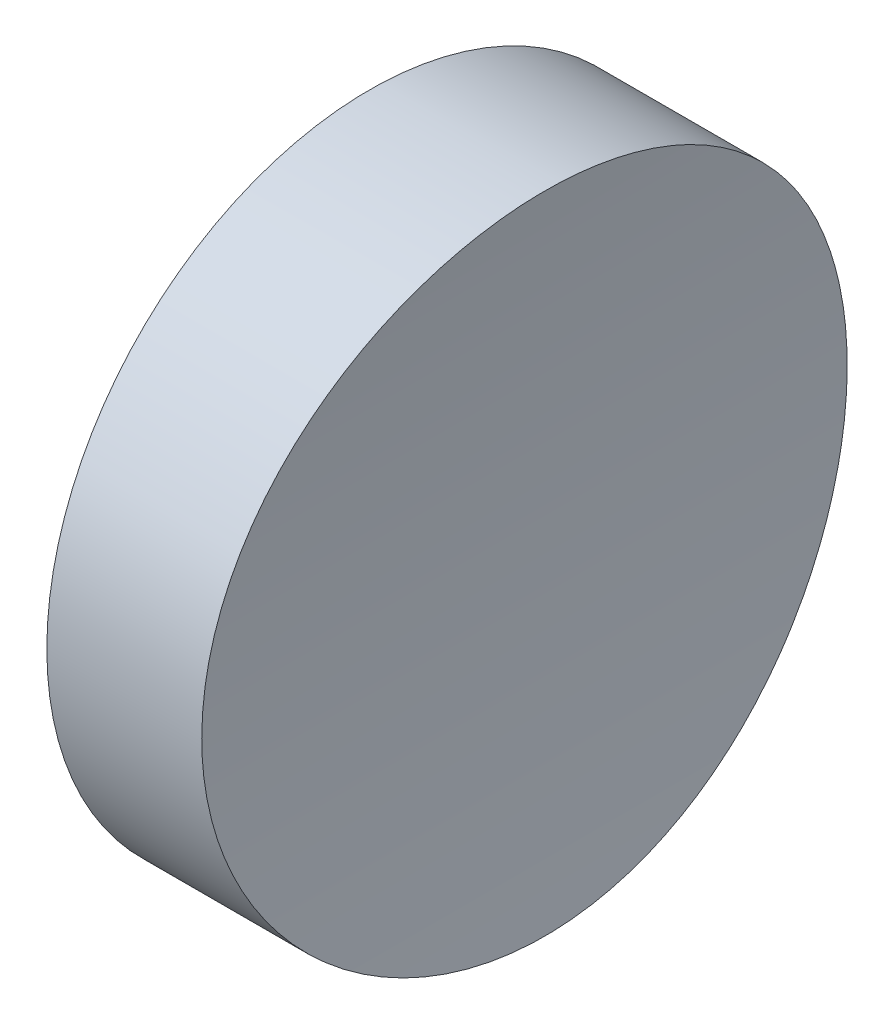
SolidWorks part; units mm, degrees
ref_plane "前视基准面" through (0, 0, 0) normal (0, 0, 1) x (1, 0, 0)
ref_plane "上视基准面" through (0, 0, 0) normal (0, 1, 0) x (1, 0, 0)
ref_plane "右视基准面" through (0, 0, 0) normal (1, 0, 0) x (0, 0, -1)
sketch "草图1" plane through (0, 0, 0) normal (1, 0, 0) x (0, 0, -1)
  circle A0 centre (0, 0) radius 6.25
  dimension "D1" = 12.5
extrude "凸台-拉伸1" add sketch "草图1" along normal blind 10
sketch "草图2" plane through (0, 0, 0) normal (0, 0, 1) x (1, 0, 0)
  line L0 (0, 0) -> (53, 0) construction
  line L1 (0, 0) -> (3, 0) construction
  circle A0 centre (53, 0) radius 50
  dimension "D1" = 100
  dimension "D2" = 3
extrude "切除-拉伸1" cut sketch "草图2" against normal through all both and the other way through all
